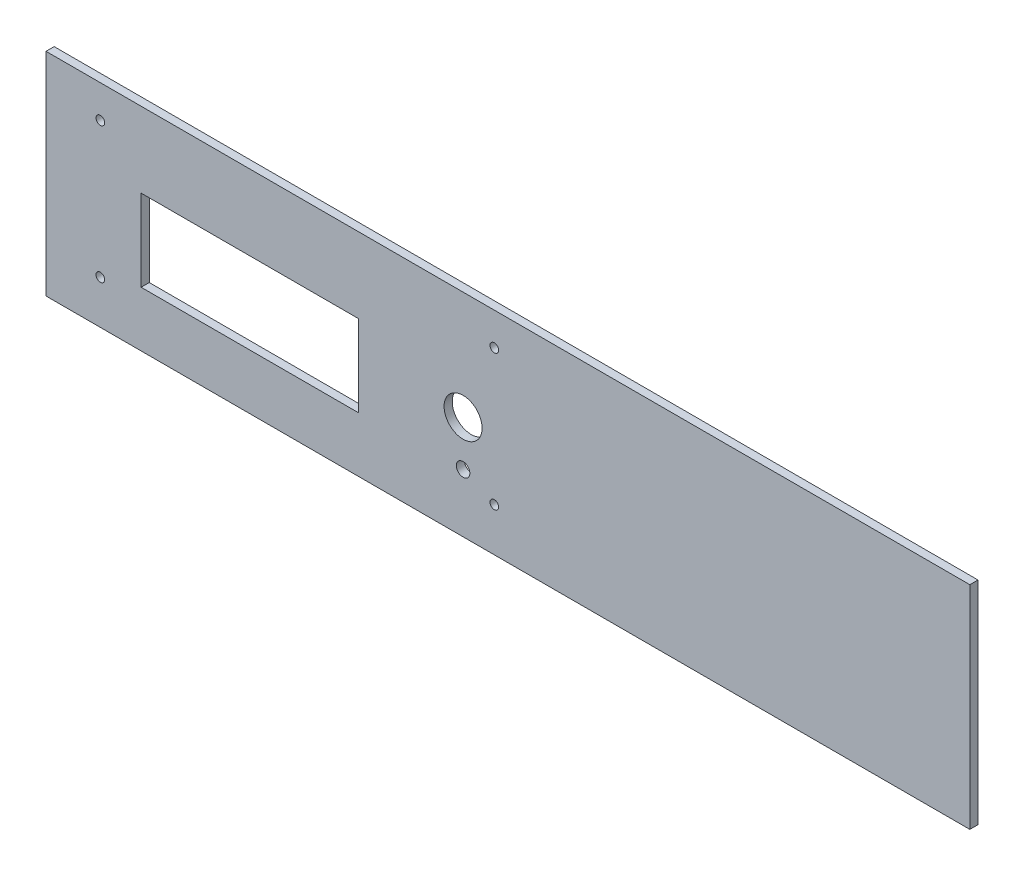
SolidWorks part; units mm, degrees
ref_plane "Plan de face" through (0, 0, 0) normal (0, 0, 1) x (1, 0, 0)
ref_plane "Plan de dessus" through (0, 0, 0) normal (0, 1, 0) x (1, 0, 0)
ref_plane "Plan de droite" through (0, 0, 0) normal (1, 0, 0) x (0, 0, -1)
sketch "Esquisse1" plane through (0, 0, 0) normal (0, 0, 1) x (1, 0, 0)
  line L1 (-170, 39) -> (170, 39)
  line L2 (-170, 39) -> (-170, -39)
  line L3 (-170, -39) -> (170, -39)
  line L4 (170, 39) -> (170, -39)
  dimension "D1" = 340
  dimension "D2" = 170
  dimension "D3" = 78
  dimension "D4" = 39
extrude "Boss.-Extru.1" add sketch "Esquisse1" along normal blind 3
sketch "Esquisse2" plane through (0, 0, 3) normal (0, 0, 1) x (1, 0, 0)
  line L0 (170, 39) -> (-170, 39) construction
  line L1 (-170, 39) -> (-170, -39) construction
  circle A0 centre (-150, 27) radius 1.6
  circle A1 centre (-150, -23) radius 1.6
  circle A2 centre (-5, 27) radius 1.6
  circle A3 centre (-5, -23) radius 1.6
  dimension "D1" = 3.2
  dimension "D2" = 3.2
  dimension "D3" = 3.2
  dimension "D4" = 3.2
  dimension "D5" = 145
  dimension "D6" = 145
  dimension "D7" = 50
  dimension "D8" = 12
  dimension "D10" = 20
  dimension "D11" = 50
  dimension "D12" = 12
  dimension "D9" = 20
extrude "Enlèv. mat.-Extru.1" cut sketch "Esquisse2" against normal through all
sketch "Esquisse3" plane through (0, 0, 3) normal (0, 0, 1) x (1, 0, 0)
  line L1 (-135, 11.3) -> (-55, 11.3)
  line L2 (-135, 11.3) -> (-135, -18.7)
  line L3 (-135, -18.7) -> (-55, -18.7)
  line L4 (-55, 11.3) -> (-55, -18.7)
  circle A0 centre (-150, 27) radius 1.6 construction
  dimension "D1" = 80
  dimension "D2" = 30
  dimension "D3" = 15
  dimension "D4" = 15.7
extrude "Enlèv. mat.-Extru.2" cut sketch "Esquisse3" against normal through all
sketch "Esquisse4" plane through (0, 0, 3) normal (0, 0, 1) x (1, 0, 0)
  circle A0 centre (-16.5, -0.9) radius 7
  circle A1 centre (-16.5, -17.5) radius 2.5
  circle A2 centre (-5, 27) radius 1.6 construction
  circle A3 centre (-5, -23) radius 1.6 construction
  dimension "D1" = 11.5
  dimension "D2" = 27.9
  dimension "D3" = 11.5
  dimension "D4" = 5.5
  dimension "D5" = 14
  dimension "D6" = 5
extrude "Enlèv. mat.-Extru.3" cut sketch "Esquisse4" against normal through all
